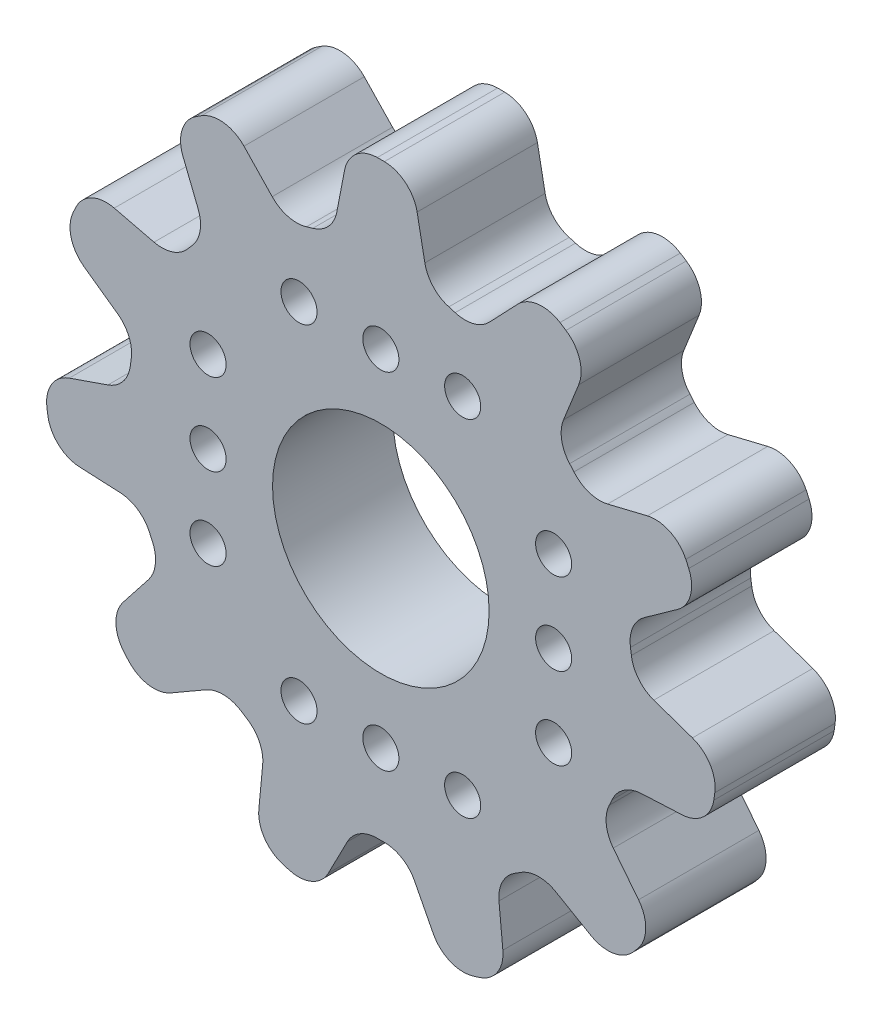
SolidWorks part; units mm, degrees
ref_plane "Plano frontal" through (0, 0, 0) normal (0, 0, 1) x (1, 0, 0)
ref_plane "Plano superior" through (0, 0, 0) normal (0, 1, 0) x (1, 0, 0)
ref_plane "Plano direito" through (0, 0, 0) normal (1, 0, 0) x (0, 0, -1)
sketch "Esboço1" plane through (0, 0, 0) normal (0, 0, 1) x (1, 0, 0)
  line L0 (4.5143, 10.4072) -> (5.687, 11.637)
  line L1 (7.5914, 8.4297) -> (8.2229, 10.0072)
  line L2 (9.4243, 6.3145) -> (11.0756, 6.7151)
  line L3 (10.9437, 2.9873) -> (12.3279, 3.973)
  line L4 (11.342, 0.2169) -> (12.9478, -0.3389)
  line L5 (10.8215, -3.4036) -> (12.5188, -3.3227)
  line L6 (9.6588, -5.9495) -> (10.7092, -7.2852)
  line L7 (7.2635, -8.7138) -> (8.7351, -9.5634)
  line L8 (4.909, -10.227) -> (5.0705, -11.9185)
  line L9 (-1.8289, 11.1957) -> (-1.5072, 12.8643)
  line L10 (1.8289, 11.1957) -> (1.5072, 12.8643)
  line L11 (1.3994, -11.2575) -> (2.1781, -12.7678)
  line L12 (-1.3994, -11.2575) -> (-2.1781, -12.7678)
  line L13 (-4.909, -10.227) -> (-5.0705, -11.9185)
  line L14 (-7.2635, -8.7138) -> (-8.7351, -9.5634)
  line L15 (-9.6588, -5.9495) -> (-10.7092, -7.2852)
  line L16 (-10.8215, -3.4036) -> (-12.5188, -3.3227)
  line L17 (-11.342, 0.2169) -> (-12.9478, -0.3389)
  line L18 (-10.9437, 2.9873) -> (-12.3279, 3.973)
  line L19 (-9.4243, 6.3145) -> (-11.0756, 6.7151)
  line L20 (-7.5914, 8.4297) -> (-8.2229, 10.0072)
  line L21 (-4.5143, 10.4072) -> (-5.687, 11.637)
  line L22 (0, 0) -> (0, 7.18) construction
  line L23 (0, 0) -> (7.18, 0) construction
  line L24 (0, 0) -> (0, -7.18) construction
  line L25 (0, 0) -> (-7.18, 0) construction
  arc A0 (0.1473, 13.9992) -> (-0.1473, 13.9992) centre (0, 0) ccw
  arc A1 (-2.8267, 10.1124) -> (-3.0892, 10.0353) centre (0, 0) ccw
  arc A2 (-2.8267, 10.1124) -> (-1.8289, 11.1957) centre (-3.2035, 11.4607) ccw
  arc A3 (2.8267, 10.1124) -> (1.8289, 11.1957) centre (3.2035, 11.4607) cw
  arc A4 (0.1473, 13.9992) -> (1.5072, 12.8643) centre (0.1325, 12.5993) cw
  arc A5 (-0.1473, 13.9992) -> (-1.5072, 12.8643) centre (-0.1325, 12.5993) ccw
  arc A6 (7.6925, 11.6973) -> (7.4447, 11.8565) centre (0, 0) ccw
  arc A7 (3.0892, 10.0353) -> (4.5143, 10.4072) centre (3.5011, 11.3733) ccw
  arc A8 (7.8451, 6.9789) -> (7.5914, 8.4297) centre (8.8911, 7.9094) cw
  arc A9 (7.6925, 11.6973) -> (8.2229, 10.0072) centre (6.9232, 10.5275) cw
  arc A10 (7.4447, 11.8565) -> (5.687, 11.637) centre (6.7002, 10.6709) ccw
  arc A11 (12.7953, 5.6815) -> (12.673, 5.9495) centre (0, 0) ccw
  arc A12 (8.0243, 6.7721) -> (9.4243, 6.3145) centre (9.0942, 7.675) ccw
  arc A13 (10.3728, 1.6296) -> (10.9437, 2.9873) centre (11.7558, 1.8469) cw
  arc A14 (12.7953, 5.6815) -> (12.3279, 3.973) centre (11.5158, 5.1134) cw
  arc A15 (12.673, 5.9495) -> (11.0756, 6.7151) centre (11.4057, 5.3545) ccw
  arc A16 (13.8358, -2.1381) -> (13.8777, -1.8465) centre (0, 0) ccw
  arc A17 (10.4117, 1.3587) -> (11.342, 0.2169) centre (11.7999, 1.5399) ccw
  arc A18 (9.6072, -4.237) -> (10.8215, -3.4036) centre (10.8881, -4.802) cw
  arc A19 (13.8358, -2.1381) -> (12.5188, -3.3227) centre (12.4522, -1.9243) cw
  arc A20 (13.8777, -1.8465) -> (12.9478, -0.3389) centre (12.4899, -1.6619) ccw
  arc A21 (10.4835, -9.2788) -> (10.6764, -9.0562) centre (0, 0) ccw
  arc A22 (9.4935, -4.4859) -> (9.6588, -5.9495) centre (10.7593, -5.0841) ccw
  arc A23 (5.7913, -8.7584) -> (7.2635, -8.7138) centre (6.5635, -9.9262) cw
  arc A24 (10.4835, -9.2788) -> (8.7351, -9.5634) centre (9.4351, -8.351) cw
  arc A25 (10.6764, -9.0562) -> (10.7092, -7.2852) centre (9.6087, -8.1506) ccw
  arc A26 (3.8027, -13.4737) -> (4.0853, -13.3907) centre (0, 0) ccw
  arc A27 (5.5611, -8.9064) -> (4.909, -10.227) centre (6.3026, -10.0939) ccw
  arc A28 (0.1368, -10.4991) -> (1.3994, -11.2575) centre (0.1551, -11.899) cw
  arc A29 (3.8027, -13.4737) -> (2.1781, -12.7678) centre (3.4225, -12.1263) cw
  arc A30 (4.0853, -13.3907) -> (5.0705, -11.9185) centre (3.6768, -12.0516) ccw
  arc A31 (-4.0853, -13.3907) -> (-3.8027, -13.4737) centre (0, 0) ccw
  arc A32 (-0.1368, -10.4991) -> (-1.3994, -11.2575) centre (-0.1551, -11.899) ccw
  arc A33 (-5.5611, -8.9064) -> (-4.909, -10.227) centre (-6.3026, -10.0939) cw
  arc A34 (-4.0853, -13.3907) -> (-5.0705, -11.9185) centre (-3.6768, -12.0516) cw
  arc A35 (-3.8027, -13.4737) -> (-2.1781, -12.7678) centre (-3.4225, -12.1263) ccw
  arc A36 (-10.6764, -9.0562) -> (-10.4835, -9.2788) centre (0, 0) ccw
  arc A37 (-5.7913, -8.7584) -> (-7.2635, -8.7138) centre (-6.5635, -9.9262) ccw
  arc A38 (-9.4935, -4.4859) -> (-9.6588, -5.9495) centre (-10.7593, -5.0841) cw
  arc A39 (-10.6764, -9.0562) -> (-10.7092, -7.2852) centre (-9.6087, -8.1506) cw
  arc A40 (-10.4835, -9.2788) -> (-8.7351, -9.5634) centre (-9.4351, -8.351) ccw
  arc A41 (-13.8777, -1.8465) -> (-13.8358, -2.1381) centre (0, 0) ccw
  arc A42 (-9.6072, -4.237) -> (-10.8215, -3.4036) centre (-10.8881, -4.802) ccw
  arc A43 (-10.4117, 1.3587) -> (-11.342, 0.2169) centre (-11.7999, 1.5399) cw
  arc A44 (-13.8777, -1.8465) -> (-12.9478, -0.3389) centre (-12.4899, -1.6619) cw
  arc A45 (-13.8358, -2.1381) -> (-12.5188, -3.3227) centre (-12.4522, -1.9243) ccw
  arc A46 (-12.673, 5.9495) -> (-12.7953, 5.6815) centre (0, 0) ccw
  arc A47 (-10.3728, 1.6296) -> (-10.9437, 2.9873) centre (-11.7558, 1.8469) ccw
  arc A48 (-8.0243, 6.7721) -> (-9.4243, 6.3145) centre (-9.0942, 7.675) cw
  arc A49 (-12.673, 5.9495) -> (-11.0756, 6.7151) centre (-11.4057, 5.3545) cw
  arc A50 (-12.7953, 5.6815) -> (-12.3279, 3.973) centre (-11.5158, 5.1134) ccw
  arc A51 (-7.4447, 11.8565) -> (-7.6925, 11.6973) centre (0, 0) ccw
  arc A52 (-7.8451, 6.9789) -> (-7.5914, 8.4297) centre (-8.8911, 7.9094) ccw
  arc A53 (-3.0892, 10.0353) -> (-4.5143, 10.4072) centre (-3.5011, 11.3733) cw
  arc A54 (-7.4447, 11.8565) -> (-5.687, 11.637) centre (-6.7002, 10.6709) cw
  arc A55 (-7.6925, 11.6973) -> (-8.2229, 10.0072) centre (-6.9232, 10.5275) ccw
  arc A56 (3.0892, 10.0353) -> (2.8267, 10.1124) centre (0, 0) ccw
  arc A57 (8.0243, 6.7721) -> (7.8451, 6.9789) centre (0, 0) ccw
  arc A58 (10.4117, 1.3587) -> (10.3728, 1.6296) centre (0, 0) ccw
  arc A59 (9.4935, -4.4859) -> (9.6072, -4.237) centre (0, 0) ccw
  arc A60 (5.5611, -8.9064) -> (5.7913, -8.7584) centre (0, 0) ccw
  arc A61 (-0.1368, -10.4991) -> (0.1368, -10.4991) centre (0, 0) ccw
  arc A62 (-5.7913, -8.7584) -> (-5.5611, -8.9064) centre (0, 0) ccw
  arc A63 (-9.6072, -4.237) -> (-9.4935, -4.4859) centre (0, 0) ccw
  arc A64 (-10.3728, 1.6296) -> (-10.4117, 1.3587) centre (0, 0) ccw
  arc A65 (-7.8451, 6.9789) -> (-8.0243, 6.7721) centre (0, 0) ccw
  arc A66 (-7.8451, 6.9789) -> (-8.0243, 6.7721) centre (0, 0) ccw
  circle A67 centre (0, 0) radius 4.5
  arc A68 (-2.8267, 10.1124) -> (-3.0892, 10.0353) centre (0, 0) ccw
  arc A69 (3.0892, 10.0353) -> (2.8267, 10.1124) centre (0, 0) ccw
  arc A70 (8.0243, 6.7721) -> (7.8451, 6.9789) centre (0, 0) ccw
  arc A71 (10.4117, 1.3587) -> (10.3728, 1.6296) centre (0, 0) ccw
  arc A72 (9.4935, -4.4859) -> (9.6072, -4.237) centre (0, 0) ccw
  arc A73 (5.5611, -8.9064) -> (5.7913, -8.7584) centre (0, 0) ccw
  arc A74 (-0.1368, -10.4991) -> (0.1368, -10.4991) centre (0, 0) ccw
  arc A75 (-5.7913, -8.7584) -> (-5.5611, -8.9064) centre (0, 0) ccw
  arc A76 (-9.6072, -4.237) -> (-9.4935, -4.4859) centre (0, 0) ccw
  arc A77 (-10.3728, 1.6296) -> (-10.4117, 1.3587) centre (0, 0) ccw
  circle A78 centre (3.4, 7.18) radius 0.75
  circle A79 centre (0, 7.18) radius 0.75
  circle A80 centre (-3.4, 7.18) radius 0.75
  circle A81 centre (7.18, -3.4) radius 0.75
  circle A82 centre (7.18, 0) radius 0.75
  circle A83 centre (7.18, 3.4) radius 0.75
  circle A84 centre (-3.4, -7.18) radius 0.75
  circle A85 centre (0, -7.18) radius 0.75
  circle A86 centre (3.4, -7.18) radius 0.75
  circle A87 centre (-7.18, 3.4) radius 0.75
  circle A88 centre (-7.18, 0) radius 0.75
  circle A89 centre (-7.18, -3.4) radius 0.75
  point P138 (0, 0)
  point P142 (0, 7.18)
  point P160 (7.18, 0)
  point P174 (0, -7.18)
  point P187 (-7.18, 0)
  point P190 (0, 0)
  dimension "D1" = 1.4
  dimension "D2" = 4
extrude "Ressalto-extrusão1" add sketch "Esboço1" along normal blind 5 contours A52 A65 A48 L19 A49 A46 A50 L18 A47 A64 A43 L17 A44 A41 A45 L16 A42 A63 A38 L15 A39 A36 A40 L14 A37 A62 A33 L13 A34 A31 A35 L12 A32 A61 A28 L11 A29 A26 A30 L8 A27 A60 A23 L7 A24 A21 A25 L6 A22 A59 A18
sketch "Esboço2" plane through (0, 0, 5) normal (0, 0, 1) x (1, 0, 0)
  circle A0 centre (0, 0) radius 10.5
  circle A1 centre (0, 0) radius 4.5
